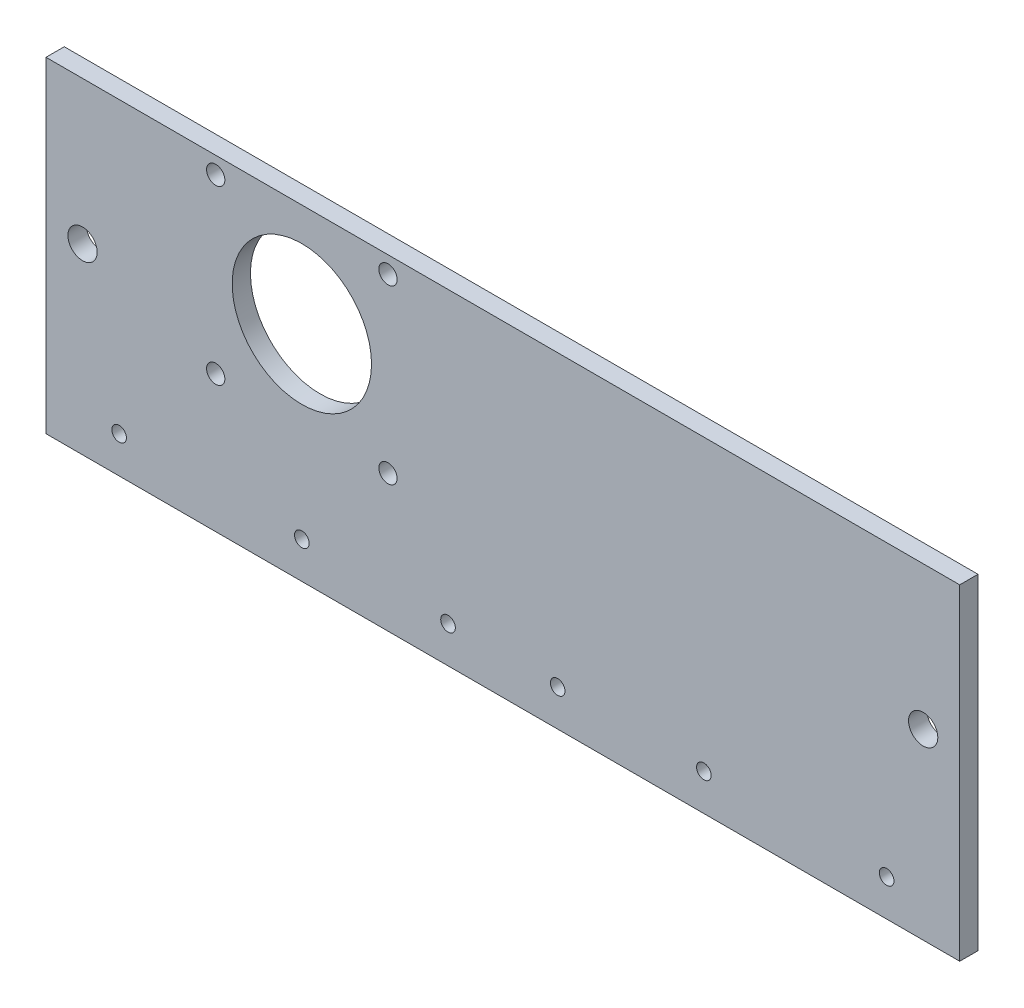
SolidWorks part; units mm, degrees
ref_plane "Ebene vorne" through (0, 0, 0) normal (0, 0, 1) x (1, 0, 0)
ref_plane "Ebene oben" through (0, 0, 0) normal (0, 1, 0) x (1, 0, 0)
ref_plane "Ebene rechts" through (0, 0, 0) normal (1, 0, 0) x (0, 0, -1)
sketch "Skizze1" plane through (0, 0, 0) normal (0, 0, 1) x (1, 0, 0)
  line L1 (0, 0) -> (250, 0)
  line L2 (0, 0) -> (0, 89.2)
  line L3 (0, 89.2) -> (250, 89.2)
  line L4 (250, 0) -> (250, 89.2)
  dimension "D1" = 89.2
  dimension "D2" = 250
extrude "Aufsatz-Linear austragen1" add sketch "Skizze1" along normal blind 5
sketch "Skizze2" plane through (0, 0, 5) normal (0, 0, 1) x (1, 0, 0)
  line L0 (0, 0) -> (250, 0) construction
  line L2 (0, 89.2) -> (0, 0) construction
  line L3 (250, 0) -> (250, 89.2) construction
  line L4 (250, 0) -> (250, 89.2) construction
  circle A0 centre (20, 10) radius 2
  circle A1 centre (70, 10) radius 2
  circle A2 centre (110, 10) radius 2
  circle A3 centre (140, 10) radius 2
  circle A4 centre (180, 10) radius 2
  circle A5 centre (230, 10) radius 2
  circle A6 centre (240, 50) radius 4
  circle A7 centre (10, 50) radius 4
  dimension "D2" = 4
  dimension "D12" = 8
  dimension "D1" = 10
  dimension "D3" = 20
  dimension "D4" = 20
  dimension "D5" = 70
  dimension "D6" = 70
  dimension "D7" = 110
  dimension "D8" = 110
  dimension "D9" = 50
  dimension "D10" = 10
  dimension "D11" = 10
extrude "Schnitt-Linear austragen1" cut sketch "Skizze2" against normal blind 27
sketch "Skizze3" plane through (0, 0, 5) normal (0, 0, 1) x (1, 0, 0)
  line L1 (250, 89.2) -> (0, 89.2) construction
  line L2 (0, 89.2) -> (0, 0) construction
  circle A0 centre (93.57, 84.57) radius 2.5
  circle A1 centre (46.43, 84.57) radius 2.5
  circle A2 centre (46.43, 37.43) radius 2.5
  circle A3 centre (93.57, 37.43) radius 2.5
  dimension "D1" = 5
  dimension "D2" = 46.43
  dimension "D3" = 4.63
  dimension "D4" = 47.14
  dimension "D5" = 47.14
extrude "Schnitt-Linear austragen2" cut sketch "Skizze3" against normal blind 27
sketch "Skizze4" plane through (0, 0, 5) normal (0, 0, 1) x (1, 0, 0)
  line L0 (250, 89.2) -> (0, 89.2) construction
  line L3 (0, 89.2) -> (0, 0) construction
  circle A0 centre (70, 61) radius 19.0625
  dimension "D1" = 38.125
  dimension "D2" = 28.2
  dimension "D3" = 70
extrude "Schnitt-Linear austragen3" cut sketch "Skizze4" against normal blind 27
